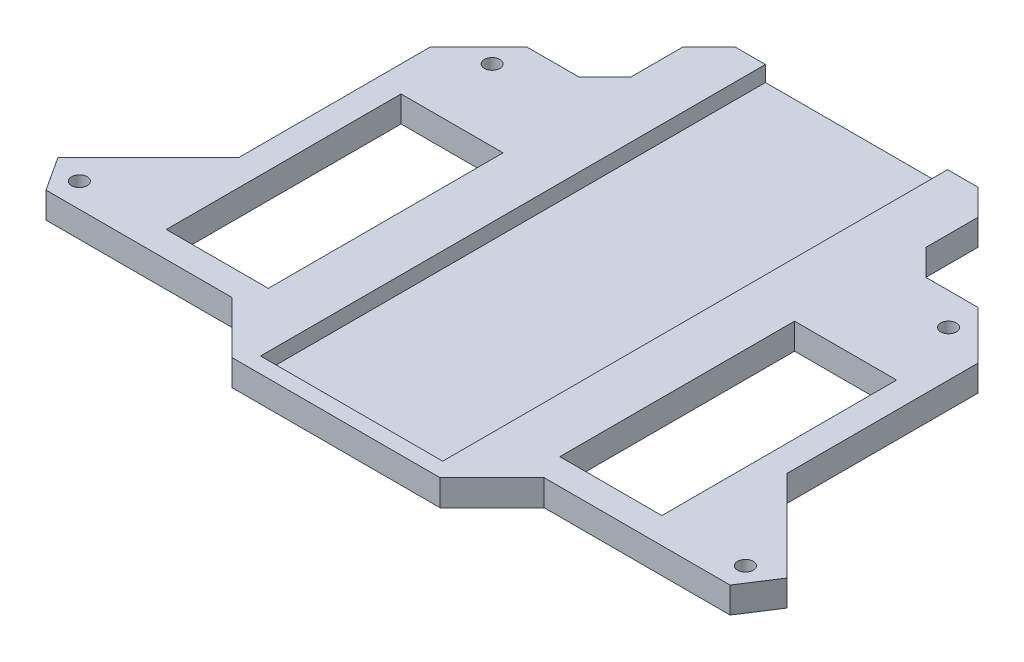
SolidWorks part; units mm, degrees
ref_plane "Front Plane" through (0, 0, 0) normal (0, 0, 1) x (1, 0, 0)
ref_plane "Top Plane" through (0, 0, 0) normal (0, 1, 0) x (1, 0, 0)
ref_plane "Right Plane" through (0, 0, 0) normal (1, 0, 0) x (0, 0, -1)
sketch "Sketch1" plane through (0, 0, 0) normal (0, 1, 0) x (1, 0, 0)
  line L0 (-59.2137, -30) -> (-70, -13.3906)
  line L1 (-70, -13.3906) -> (-70, 23.3381)
  line L2 (-70, 23.3381) -> (-23.3381, 70)
  line L4 (0, -30) -> (0, 70)
  line L5 (0, -30) -> (-59.2137, -30)
  line L6 (-59.397, 28.2843) -> (-43.8406, 43.8406) construction
  line L7 (-51.9976, -33.7676) -> (-63.9796, -15.3169) construction
  line L8 (-23.3381, 70) -> (0, 70)
  line L9 (0, 0) -> (-85, 0) construction
  line L10 (-43.8406, 43.8406) -> (0, 0) construction
  line L11 (-51.9976, -33.7676) -> (0, 0) construction
  line L12 (-47.6, 30.1) -> (-28, 30.1)
  line L13 (-47.6, 30.1) -> (-47.6, -15)
  line L14 (-47.6, -15) -> (-28, -15)
  line L15 (-28, 30.1) -> (-28, -15)
  circle A0 centre (0, 0) radius 85 construction
  circle A1 centre (-43.8406, 43.8406) radius 1.5
  circle A4 centre (-63.9796, -15.3169) radius 1.5
  dimension "D7" = 3
  dimension "D17" = 170
  dimension "D3" = 4
  dimension "D5" = 30
  dimension "D6" = 70
  dimension "D8" = 62
  dimension "D9" = 22
  dimension "D10" = 22
  dimension "D11" = 19.6
  dimension "D12" = 45.1
  dimension "D13" = 28
  dimension "D14" = 45
  dimension "D15" = 33
  dimension "D16" = 15
  dimension "D18" = 4
  dimension "D19" = 70
extrude "Boss-Extrude1" add sketch "Sketch1" along normal blind 5
sketch "Sketch3" plane through (0, 5, 0) normal (0, 1, 0) x (1, 0, 0)
  line L0 (-20, -30) -> (-30, -20)
  line L1 (-59.2137, -30) -> (0, -30) construction
  line L2 (-30, -20) -> (-65.7078, -20)
  line L3 (-70, -13.3906) -> (-59.2137, -30) construction
  line L4 (-65.7078, -20) -> (-70, -13.3906)
  line L5 (-70, -13.3906) -> (-52.6, 4.0094)
  line L6 (-52.6, 4.0094) -> (-52.6, 40.7381)
  line L7 (-23.3381, 70) -> (-70, 23.3381) construction
  line L8 (-52.6, 40.7381) -> (-43.3381, 50)
  line L9 (-43.3381, 50) -> (-33.3381, 50)
  line L10 (-33.3381, 50) -> (-28.3381, 55)
  line L11 (-28.3381, 55) -> (-28.3381, 65)
  line L12 (-28.3381, 65) -> (-75, 65)
  line L13 (-75, 65) -> (-75, -30)
  line L14 (-75, -30) -> (-20, -30)
  line L15 (0, -30) -> (0, 70) construction
  line L16 (-70, 23.3381) -> (-70, -13.3906) construction
  line L17 (-47.6, 30.1) -> (-47.6, -15) construction
  line L19 (0, 70) -> (-23.3381, 70) construction
  dimension "D1" = 20
  dimension "D2" = 10
  dimension "D3" = 45
  dimension "D4" = 45
  dimension "D5" = 5
  dimension "D6" = 20
  dimension "D7" = 5
  dimension "D8" = 5
  dimension "D9" = 5
extrude "Cut-Extrude2" cut sketch "Sketch3" against normal up to next (5 mm away)
mirror "Mirror1" about plane through (0, 5, 30) normal (-1, 0, 0) of "Cut-Extrude2", "Boss-Extrude1"
sketch "Sketch2" plane through (0, 5, 0) normal (0, 1, 0) x (1, 0, 0)
  line L0 (23.3381, 70) -> (-23.3381, 70) construction
  line L1 (-17.5, 70) -> (17.5, 70)
  line L2 (-17.5, 70) -> (-17.5, -27)
  line L3 (-17.5, -27) -> (17.5, -27)
  line L4 (17.5, 70) -> (17.5, -27)
  line L5 (-20, -30) -> (20, -30) construction
  dimension "D1" = 3
  dimension "D2" = 35
  dimension "D3" = 17.5
extrude "Cut-Extrude1" cut sketch "Sketch2" against normal blind 3
